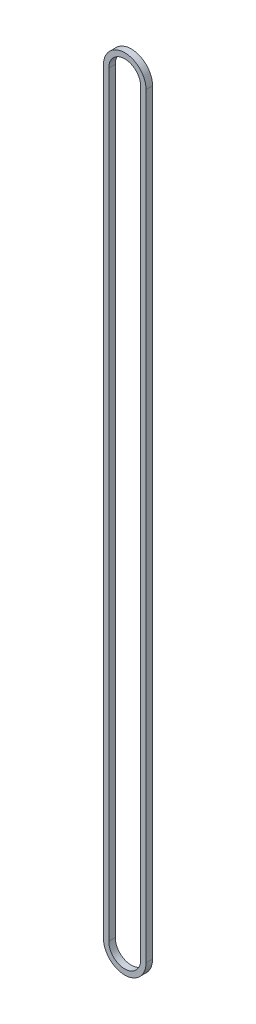
SolidWorks part; units mm, degrees
ref_plane "Front Plane" through (0, 0, 0) normal (0, 0, 1) x (1, 0, 0)
ref_plane "Top Plane" through (0, 0, 0) normal (0, 1, 0) x (1, 0, 0)
ref_plane "Right Plane" through (0, 0, 0) normal (1, 0, 0) x (0, 0, -1)
sketch "Sketch1" plane through (0, 0, 0) normal (0, 0, 1) x (1, 0, 0)
  line L0 (0, 0) -> (0, 901.7) construction
  line L1 (-19.05, 0) -> (-19.05, 901.7)
  line L2 (19.05, 0) -> (19.05, 901.7)
  line L3 (-25.4, 0) -> (-25.4, 901.7)
  line L4 (25.4, 0) -> (25.4, 901.7)
  line L5 (0, -19.05) -> (0, -25.4) construction
  arc A0 (-19.05, 0) -> (19.05, 0) centre (0, 0) ccw
  arc A1 (19.05, 901.7) -> (-19.05, 901.7) centre (0, 901.7) ccw
  arc A2 (25.4, 901.7) -> (-25.4, 901.7) centre (0, 901.7) ccw
  arc A3 (-25.4, 0) -> (25.4, 0) centre (0, 0) ccw
  point P3 (0, 450.85)
  point P16 (0, -22.225)
  dimension "D1" = 22.225
  dimension "D2" = 901.7
  dimension "D3" = 6.35
extrude "Boss-Extrude1" add sketch "Sketch1" along normal blind 7.7978
